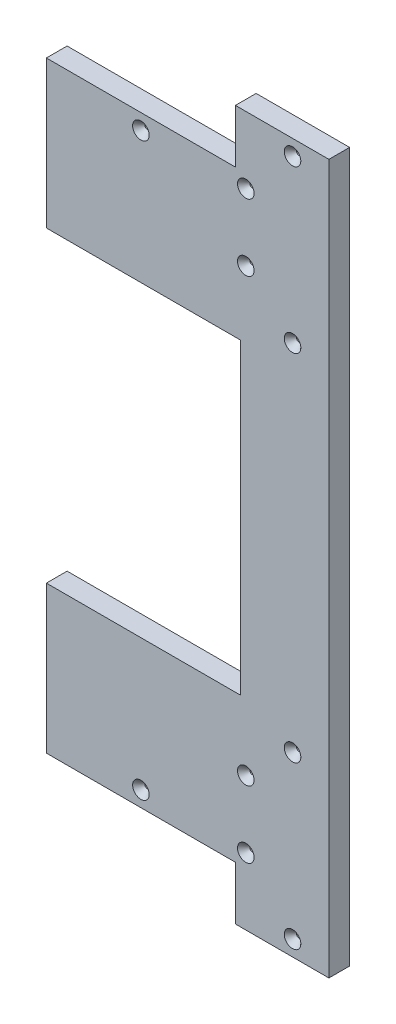
SolidWorks part; units mm, degrees
material "Beech"
ref_plane "Front Plane" through (0, 0, 0) normal (0, 0, 1) x (1, 0, 0)
ref_plane "Top Plane" through (0, 0, 0) normal (0, 1, 0) x (1, 0, 0)
ref_plane "Right Plane" through (0, 0, 0) normal (1, 0, 0) x (0, 0, -1)
sketch "Sketch1" plane through (0, 0, 0) normal (0, 0, 1) x (1, 0, 0)
  line L1 (-81.8518, 217.3) -> (116.731, 217.3)
  line L2 (-81.8518, 217.3) -> (-81.8518, -217.3)
  line L3 (-81.8518, -217.3) -> (116.731, -217.3)
  line L4 (116.731, 217.3) -> (116.731, -217.3)
  line L5 (72.1361, 217.3) -> (161.737, 217.3) construction
  point P4 (0, 0)
  point P8 (40.3861, -217.3)
extrude "Boss-Extrude1" add sketch "Sketch1" along normal blind 12.7
sketch "Sketch2" plane through (0, 0, 0) normal (0, 0, -1) x (-1, 0, 0)
  line L1 (-59.4361, 184.525) -> (81.8518, 184.525)
  line L2 (-59.4361, 184.525) -> (-59.4361, 217.3)
  line L3 (-59.4361, 217.3) -> (81.8518, 217.3)
  line L4 (81.8518, 184.525) -> (81.8518, 217.3)
  line L5 (-59.4361, -184.525) -> (81.8518, -184.525)
  line L6 (-59.4361, -184.525) -> (-59.4361, -217.3)
  line L7 (-59.4361, -217.3) -> (81.8518, -217.3)
  line L8 (81.8518, -184.525) -> (81.8518, -217.3)
extrude "Cut-Extrude1" cut sketch "Sketch2" against normal up to next
sketch "Sketch3" plane through (0, 0, 12.7) normal (0, 0, 1) x (1, 0, 0)
  line L0 (-81.8518, 184.525) -> (-81.8518, -184.525) construction
  line L1 (59.4361, 91.075) -> (-81.8518, 91.075) construction
  line L2 (59.4361, 91.075) -> (59.4361, -91.075) construction
  line L3 (59.4361, -91.075) -> (-81.8518, -91.075) construction
  line L4 (-81.8518, 91.075) -> (-81.8518, -91.075) construction
  line L5 (-81.8518, 91.075) -> (59.4361, 91.075) construction
  line L6 (-81.8518, -91.075) -> (59.4361, -91.075) construction
  line L7 (59.4361, 165.475) -> (59.4361, -165.475) construction
  line L8 (62.6111, 94.25) -> (-56.4518, 94.25)
  line L9 (-85.0268, 94.25) -> (-85.0268, -94.25)
  line L10 (62.6111, -94.25) -> (-56.4518, -94.25)
  line L11 (62.6111, 94.25) -> (62.6111, -94.25)
  line L12 (-81.8518, 94.25) -> (-85.0268, 94.25)
  line L13 (-81.8518, 184.525) -> (-56.4518, 184.525)
  line L14 (-81.8518, 184.525) -> (-81.8518, 94.25)
  line L16 (-56.4518, 184.525) -> (-56.4518, 94.25)
  line L17 (62.6111, 94.25) -> (-85.0268, 94.25) construction
  line L18 (-81.8518, -94.25) -> (-85.0268, -94.25)
  line L19 (-81.8518, -184.525) -> (-56.4518, -184.525)
  line L20 (-81.8518, -184.525) -> (-81.8518, -94.25)
  line L22 (-56.4518, -184.525) -> (-56.4518, -94.25)
  line L23 (62.6111, -94.25) -> (-85.0268, -94.25) construction
  dimension "D2" = 25.4
  dimension "D1" = 3.175
extrude "Cut-Extrude2" cut sketch "Sketch3" against normal up to next
hole_wizard "Hole1" positions "Sketch4" profile "Sketch5" legacy
sketch "Sketch4" plane through (449.8285, 0, 12.7) normal (0, 0, 1) x (0, 1, 0)
  line L0 (207.775, 377.6924) -> (207.775, 333.0975) construction
  line L4 (108.65, 377.6924) -> (108.65, 333.0975) construction
  line L8 (175, 506.2803) -> (175, 390.3924) construction
  line L12 (94.25, 390.3924) -> (94.25, 377.6924) construction
  line L17 (94.25, 384.0424) -> (217.3, 384.0424) construction
  line L19 (94.25, 384.0424) -> (135.2667, 384.0424)
  line L20 (135.2667, 384.0424) -> (176.2833, 384.0424)
  line L21 (176.2833, 384.0424) -> (217.3, 384.0424)
  line L22 (0, 333.0975) -> (0, 390.3924) construction
  point P39 (108.65, 355.3949)
  point P41 (207.775, 355.3949)
  point P43 (175, 448.3363)
  point P47 (135.2667, 384.0424)
  point P49 (176.2833, 384.0424)
  point P65 (-175, 448.3363)
  point P66 (-135.2667, 384.0424)
  point P67 (-176.2833, 384.0424)
  point P68 (-207.775, 355.3949)
  point P69 (-108.65, 355.3949)
  point P71 (0, 0)
  point P72 (108.65, 333.0975)
  point P73 (0, 0)
  point P74 (207.775, 333.0975)
sketch "Sketch5" plane through (94.4335, -108.65, 12.7) normal (1, 0, 0) x (0, -1, 0)
  line L0 (0, 0) -> (0, 39.0539)
  line L1 (0, 39.0539) -> (1.5875, 38.1)
  line L2 (1.5875, 38.1) -> (1.5875, 4.0177)
  line L3 (1.5875, 4.0177) -> (5.08, 0)
  line L4 (5.08, 0) -> (0, 0)
  line L5 (0, -14.3089) -> (0, 102.4216) construction
  line L6 (0, 39.0539) -> (-1.5875, 38.1) construction
  line L7 (-1.5875, 4.0177) -> (-5.08, 0) construction
  dimension "Diameter" = 3.175
  dimension "Depth" = 38.1
  dimension "C-Sink Diameter" = 10.16
  dimension "C-Sink Angle" = 82
  dimension "Drill Angle" = 118
